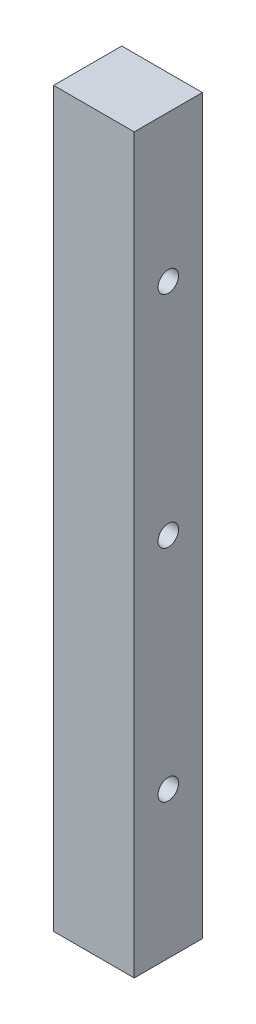
SolidWorks part; units mm, degrees
ref_plane "Front Plane" through (0, 0, 0) normal (0, 0, 1) x (1, 0, 0)
ref_plane "Top Plane" through (0, 0, 0) normal (0, 1, 0) x (1, 0, 0)
ref_plane "Right Plane" through (0, 0, 0) normal (1, 0, 0) x (0, 0, -1)
sketch "Sketch1" plane through (0, 0, 0) normal (0, 0, 1) x (1, 0, 0)
  line L1 (0, 0) -> (13.97, 0)
  line L2 (0, 0) -> (0, 127)
  line L3 (0, 127) -> (13.97, 127)
  line L4 (13.97, 0) -> (13.97, 127)
  dimension "D1" = 127
  dimension "D2" = 13.97
extrude "Boss-Extrude1" add sketch "Sketch1" along normal blind 11.811
sketch "Sketch2" plane through (0, 0, 0) normal (-1, 0, 0) x (0, 0, 1)
  line L0 (5.9055, 127) -> (5.9055, 0) construction
  line L1 (11.811, 127) -> (0, 127) construction
  line L2 (11.811, 0) -> (0, 0) construction
  circle A0 centre (5.9055, 101.6) radius 1.778
  circle A1 centre (5.9055, 63.5) radius 1.778
  circle A2 centre (5.9055, 25.4) radius 1.778
  dimension "D1" = 3.556
  dimension "D2" = 38.1
  dimension "D3" = 38.1
  dimension "D5" = 25.4
extrude "Cut-Extrude1" cut sketch "Sketch2" against normal through all
